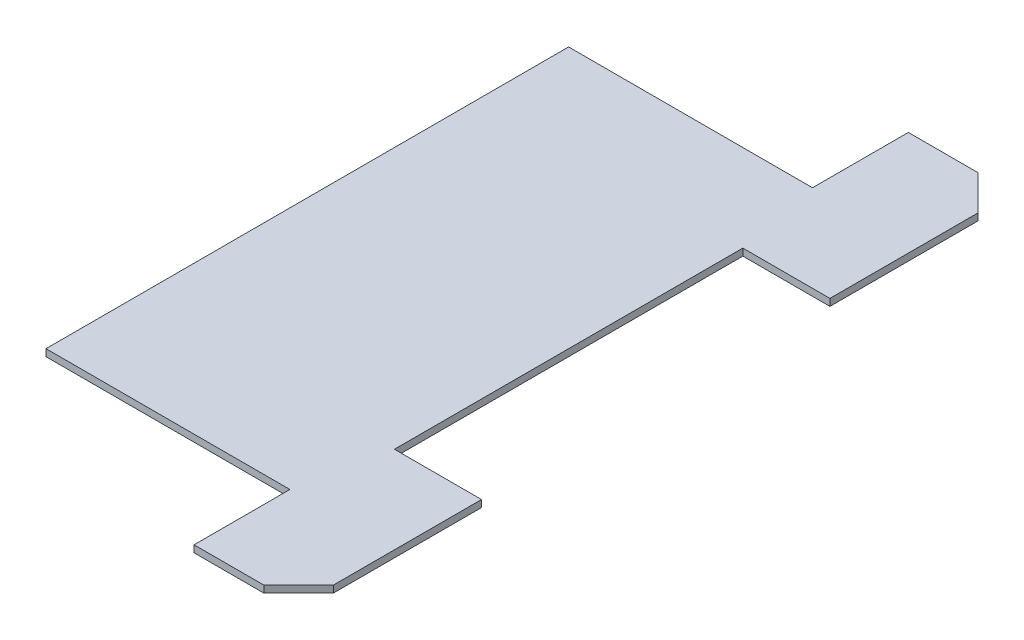
SolidWorks part; units mm, degrees
material "AISI 316 Нержавеющая сталь, лист (SS)"
ref_plane "Спереди" through (0, 0, 0) normal (0, 0, 1) x (1, 0, 0)
ref_plane "Сверху" through (0, 0, 0) normal (0, 1, 0) x (1, 0, 0)
ref_plane "Справа" through (0, 0, 0) normal (1, 0, 0) x (0, 0, -1)
sketch "Эскиз1" plane through (0, 0, 0) normal (0, 1, 0) x (1, 0, 0)
  line L0 (5, -9.25) -> (5, -5)
  line L1 (-5, 7.5) -> (-5, -7.5)
  line L2 (4, 10.25) -> (5, 9.25)
  line L3 (4, -10.25) -> (5, -9.25)
  line L4 (5, -5) -> (2.5, -5)
  line L7 (2.5, -5) -> (2.5, 5)
  line L8 (2.5, 5) -> (5, 5)
  line L9 (5, 5) -> (5, 9.25)
  line L10 (-5, 7.5) -> (2, 7.5)
  line L11 (2, 7.5) -> (2, 10.25)
  line L12 (-5, -7.5) -> (2, -7.5)
  line L13 (2, -7.5) -> (2, -10.25)
  line L15 (2, 10.25) -> (4, 10.25)
  line L16 (2, -10.25) -> (4, -10.25)
  point P0 (0, 0)
  point P1 (5, 10.25)
  point P4 (5, -10.25)
  dimension "D1" = 10
  dimension "D2" = 20.5
  dimension "D3" = 15
  dimension "D4" = 10
  dimension "D5" = 3
  dimension "D6" = 7.5
  dimension "D7" = 5
  dimension "D8" = 7.5
  dimension "D11" = 1
  dimension "D12" = 1
extrude "Бобышка-Вытянуть1" add sketch "Эскиз1" along normal blind 0.2
